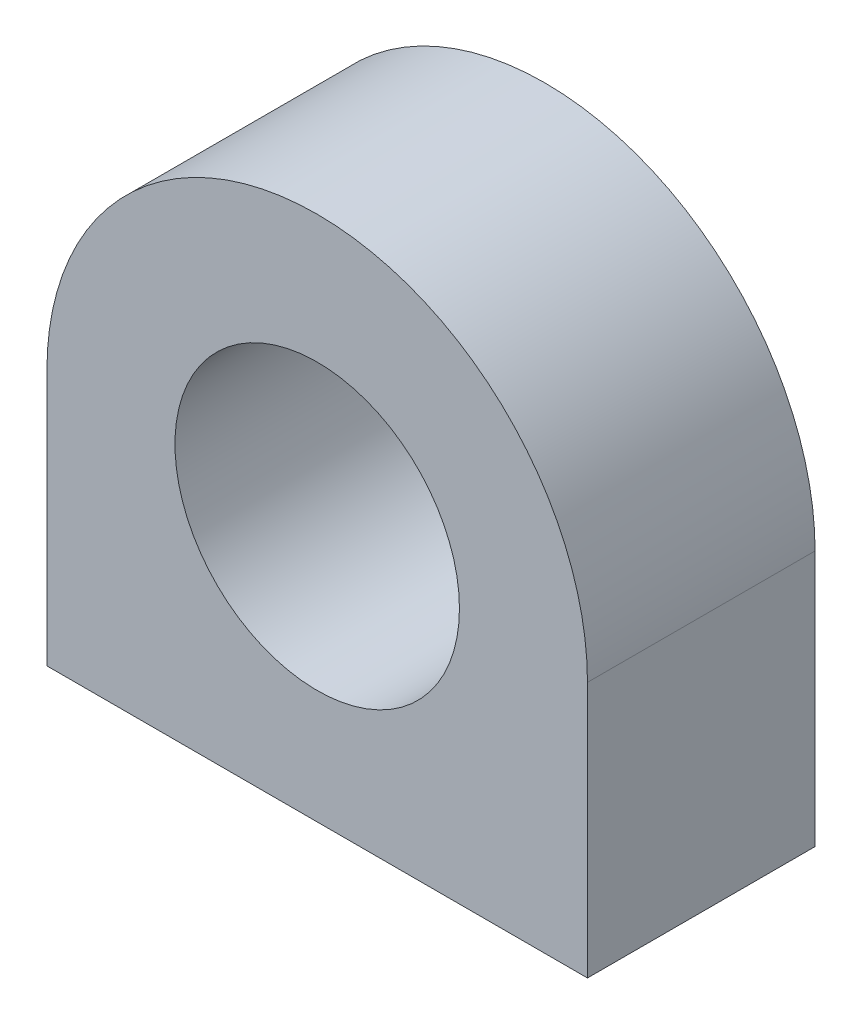
SolidWorks part; units mm, degrees
ref_plane "Front Plane" through (0, 0, 0) normal (0, 0, 1) x (1, 0, 0)
ref_plane "Top Plane" through (0, 0, 0) normal (0, 1, 0) x (1, 0, 0)
ref_plane "Right Plane" through (0, 0, 0) normal (1, 0, 0) x (0, 0, -1)
sketch "Sketch1" plane through (0, 0, 0) normal (0, 0, 1) x (1, 0, 0)
  line L0 (0, -55.1885) -> (0, 89.378) construction
  line L1 (-38, 0) -> (38, 0)
  line L2 (38, 0) -> (38, 36)
  line L3 (-38, 0) -> (-38, 36)
  arc A0 (38, 36) -> (-38, 36) centre (0, 36) ccw
  dimension "D2" = 36
extrude "Boss-Extrude1" add sketch "Sketch1" along normal blind 32
sketch "Sketch2" plane through (0, 0, 32) normal (0, 0, 1) x (1, 0, 0)
  circle A0 centre (0, 36) radius 20
  dimension "D1" = 40
extrude "Cut-Extrude1" cut sketch "Sketch2" against normal blind 32
